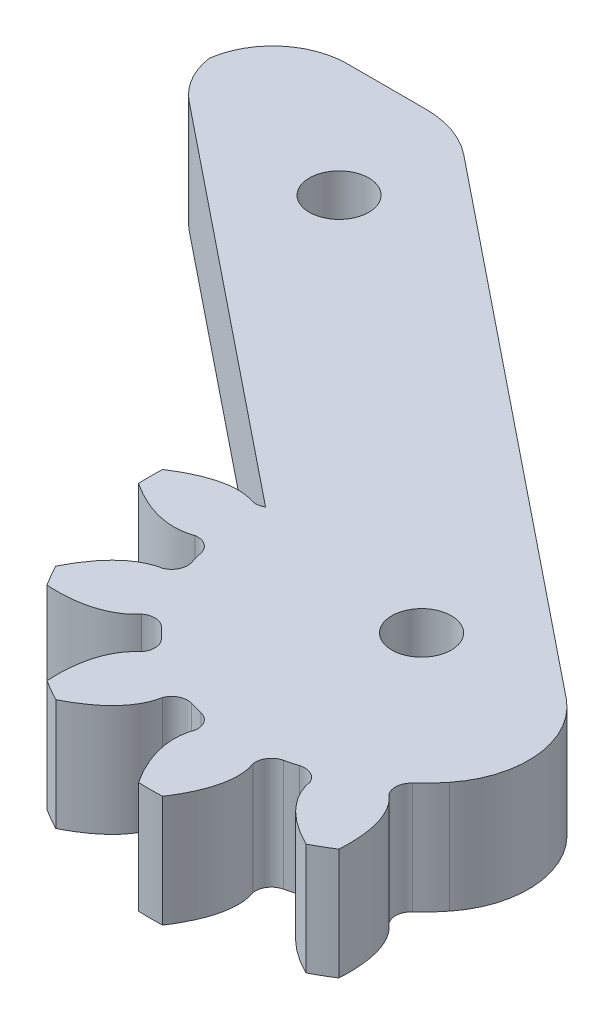
SolidWorks part; units mm, degrees
material "MDF"
ref_plane "Plano frontal" through (0, 0, 0) normal (0, 0, 1) x (1, 0, 0)
ref_plane "Plano superior" through (0, 0, 0) normal (0, 1, 0) x (1, 0, 0)
ref_plane "Plano direito" through (0, 0, 0) normal (1, 0, 0) x (0, 0, -1)
ref_plane "Plano1" through (0, -6, 0) normal (0, -1, 0) x (1, 0, 0)
sketch "Esboço1" plane through (0, -6, 0) normal (0, -1, 0) x (1, 0, 0)
  line L0 (-35.0534, -1.6658) -> (-56.006, -18.507)
  line L1 (-53.5, -24.5) -> (-49.2604, -24.5)
  line L2 (-46.1279, -23.3971) -> (-18.0516, -0.83)
  line L3 (-21.184, 3.0672) -> (-21.184, -24.5) construction
  arc A0 (-17.1566, 12.2945) -> (-39.569, -0.6453) centre (-25, 0) ccw
  arc A1 (-35.6102, -1.5602) -> (-35.0534, -1.6658) centre (-35.4833, -2.4123) cw
  arc A2 (-56.006, -18.507) -> (-57.4603, -21.0624) centre (-53.5, -21.6247) ccw
  arc A3 (-57.4603, -21.0624) -> (-53.5, -24.5) centre (-53.5, -20.5) ccw
  arc A4 (-49.2604, -24.5) -> (-46.1279, -23.3971) centre (-49.2604, -19.5) ccw
  arc A5 (-18.0516, -0.83) -> (-17.2869, 6.1996) centre (-21.184, 3.0672) ccw
  arc A6 (-17.2869, 6.1996) -> (-18.2563, 7.2422) centre (-25, 0) ccw
  arc A7 (-18.3437, 8.4086) -> (-18.2563, 7.2422) centre (-17.6692, 7.8727) ccw
  ellipse E0 centre (-40.0135, 7.1244) end of major axis (-44.7656, 15.6491) minor radius 4.8741 (-39.569, -0.6453) -> (-35.6102, -1.5602) ccw
  ellipse E1 centre (-23.6632, 16.5643) end of major axis (-18.6566, 8.1866) minor radius 4.8741 (-18.3437, 8.4086) -> (-17.1566, 12.2945) ccw
  point P3 (-40.0135, 7.1244)
  point P4 (-35.7563, 9.4976)
  point P5 (-44.7656, 15.6491)
  point P6 (-39.569, -0.6453)
  point P7 (-35.6102, -1.5602)
  point P8 (-37.6643, -1.5626)
  point P9 (-42.3628, 15.8114)
  point P32 (-23.6632, 16.5643)
  point P33 (-19.4793, 19.0646)
  point P34 (-18.6566, 8.1866)
  point P35 (-18.3437, 8.4086)
  point P36 (-17.1566, 12.2945)
  point P37 (-17.3146, 10.1863)
  point P38 (-30.0117, 22.9423)
  dimension "D5" = 4
  dimension "D1" = 24.5
  dimension "D2" = 36.0216
  dimension "D3" = 51.208
  dimension "D4" = 10
  dimension "D6" = 2.8753
  dimension "D7" = 3.9603
extrude "Ressalto-extrusão1" add sketch "Esboço1" against normal blind 6
sketch "Esboço2" plane through (0, 0, 0) normal (0, 1, 0) x (-1, 0, 0)
  arc A0 (24.3547, 14.569) -> (18.2743, 12.9398) centre (25, 0) ccw
  arc A1 (21.0461, 9.9688) -> (22.0999, 9.4613) centre (21.8474, 10.285) ccw
  arc A2 (22.0999, 9.4613) -> (22.7809, 9.6438) centre (25, 0) cw
  arc A3 (22.7809, 9.6438) -> (23.4398, 10.6102) centre (22.5877, 10.4833) ccw
  ellipse E0 centre (11.3233, 9.4399) end of major axis (1.5647, 9.2929) minor radius 4.8741 (21.0461, 9.9688) -> (18.2743, 12.9398) ccw
  ellipse E1 centre (32.1244, 15.0135) end of major axis (40.6491, 19.7656) minor radius 4.8741 (24.3547, 14.569) -> (23.4398, 10.6102) ccw
  point P3 (11.3233, 9.4399)
  point P4 (1.5647, 9.2929)
  point P5 (11.2499, 14.3134)
  point P6 (21.0461, 9.9688)
  point P7 (18.2743, 12.9398)
  point P8 (20.0211, 11.7489)
  point P9 (2.6255, 7.1309)
  point P21 (32.1244, 15.0135)
  point P22 (23.5997, 10.2615)
  point P23 (34.4976, 10.7563)
  point P24 (24.3547, 14.569)
  point P25 (23.4398, 10.6102)
  point P26 (23.4374, 12.6643)
  point P27 (40.8114, 17.3628)
extrude "Corte-extrusão1" cut sketch "Esboço2" against normal through all
sketch "Esboço3" plane through (0, 0, 0) normal (0, 1, 0) x (-1, 0, 0)
  arc A0 (31.7257, 12.9398) -> (25.6453, 14.569) centre (25, 0) ccw
  arc A1 (26.5602, 10.6102) -> (27.2191, 9.6438) centre (27.4123, 10.4833) ccw
  arc A2 (27.2191, 9.6438) -> (27.9001, 9.4613) centre (25, 0) cw
  arc A3 (27.9001, 9.4613) -> (28.9539, 9.9688) centre (28.1526, 10.285) ccw
  ellipse E0 centre (17.8756, 15.0135) end of major axis (9.3509, 19.7656) minor radius 4.8741 (26.5602, 10.6102) -> (25.6453, 14.569) ccw
  ellipse E1 centre (38.6767, 9.4399) end of major axis (48.4353, 9.2929) minor radius 4.8741 (31.7257, 12.9398) -> (28.9539, 9.9688) ccw
  point P3 (17.8756, 15.0135)
  point P4 (9.3509, 19.7656)
  point P5 (20.2488, 19.2708)
  point P6 (26.5602, 10.6102)
  point P7 (25.6453, 14.569)
  point P8 (26.5626, 12.6643)
  point P9 (9.1886, 17.3628)
  point P21 (38.6767, 9.4399)
  point P22 (28.9181, 9.5868)
  point P23 (38.6033, 4.5664)
  point P24 (31.7257, 12.9398)
  point P25 (28.9539, 9.9688)
  point P26 (29.9789, 11.7489)
  point P27 (47.3745, 7.1309)
extrude "Corte-extrusão2" cut sketch "Esboço3" against normal through all
sketch "Esboço4" plane through (0, 0, 0) normal (0, 1, 0) x (-1, 0, 0)
  arc A0 (37.2945, 7.8434) -> (32.8434, 12.2945) centre (25, 0) ccw
  arc A1 (31.6563, 8.4086) -> (31.7437, 7.2422) centre (32.3308, 7.8727) ccw
  arc A2 (31.7437, 7.2422) -> (32.2422, 6.7437) centre (25, 0) cw
  arc A3 (32.2422, 6.7437) -> (33.4086, 6.6563) centre (32.8727, 7.3308) ccw
  ellipse E0 centre (26.3368, 16.5643) end of major axis (21.3303, 24.942) minor radius 4.8741 (31.6563, 8.4086) -> (32.8434, 12.2945) ccw
  ellipse E1 centre (41.5643, 1.3368) end of major axis (33.1866, 6.3434) minor radius 4.8741 (37.2945, 7.8434) -> (33.4086, 6.6563) ccw
  point P3 (26.3368, 16.5643)
  point P4 (22.153, 14.064)
  point P5 (21.3303, 24.942)
  point P6 (31.6563, 8.4086)
  point P7 (32.8434, 12.2945)
  point P8 (32.6854, 10.1863)
  point P9 (19.9883, 22.9423)
  point P21 (41.5643, 1.3368)
  point P22 (33.1866, 6.3434)
  point P23 (39.064, -2.847)
  point P24 (37.2945, 7.8434)
  point P25 (33.4086, 6.6563)
  point P26 (35.1863, 7.6854)
  point P27 (47.9423, -5.0117)
extrude "Corte-extrusão3" cut sketch "Esboço4" against normal through all
sketch "Esboço5" plane through (0, 0, 0) normal (0, 1, 0) x (-1, 0, 0)
  arc A0 (39.569, 0.6453) -> (37.9398, 6.7257) centre (25, 0) ccw
  arc A1 (34.9688, 3.9539) -> (34.4613, 2.9001) centre (35.285, 3.1526) ccw
  arc A2 (34.4613, 2.9001) -> (34.6438, 2.2191) centre (25, 0) cw
  arc A3 (34.6438, 2.2191) -> (35.6102, 1.5602) centre (35.4833, 2.4123) ccw
  ellipse E0 centre (34.4399, 13.6767) end of major axis (34.2929, 23.4353) minor radius 4.8741 (34.9688, 3.9539) -> (37.9398, 6.7257) ccw
  ellipse E1 centre (40.0135, -7.1244) end of major axis (44.7656, -15.6491) minor radius 4.8741 (39.569, 0.6453) -> (35.6102, 1.5602) ccw
  point P3 (34.4399, 13.6767)
  point P4 (29.5664, 13.6033)
  point P5 (34.2929, 23.4353)
  point P6 (34.9688, 3.9539)
  point P7 (37.9398, 6.7257)
  point P8 (36.7489, 4.9789)
  point P9 (32.1309, 22.3745)
  point P21 (40.0135, -7.1244)
  point P22 (35.7563, -9.4976)
  point P23 (44.7656, -15.6491)
  point P24 (39.569, 0.6453)
  point P25 (35.6102, 1.5602)
  point P26 (37.6643, 1.5626)
  point P27 (42.3628, -15.8114)
extrude "Corte-extrusão4" cut sketch "Esboço5" against normal through all
sketch "Esboço6" plane through (0, -6, 0) normal (0, -1, 0) x (1, 0, 0)
  line L0 (-49.1143, -19.3826) -> (-28.0223, -2.4293) construction
  line L1 (-35.0534, -1.6658) -> (-56.006, -18.507) construction
  line L2 (-39.2648, -17.8807) -> (-45.5297, -10.0864) construction
  line L3 (-46.1279, -23.3971) -> (-18.0516, -0.83) construction
  circle A0 centre (-25, 0) radius 1.6
  arc A1 (-18.0516, -0.83) -> (-17.2869, 6.1996) centre (-21.184, 3.0672) ccw construction
  point P13 (-42.3972, -13.9835)
  dimension "D1" = 3.2
  dimension "D2" = 4.8958
extrude "Corte-extrusão5" cut sketch "Esboço6" against normal through all
sketch "Esboço7" plane through (0, 0, 0) normal (0, 1, 0) x (-1, 0, 0)
  line L0 (49.1143, -19.3826) -> (28.0223, -2.4293) construction
  line L1 (53.5, -24.5) -> (49.2604, -24.5) construction
  circle A0 centre (47.5984, -18.1641) radius 1.6
  circle A1 centre (25, 0) radius 1.6 construction
  dimension "D1" = 6.3359
extrude "Corte-extrusão6" cut sketch "Esboço7" against normal through all
